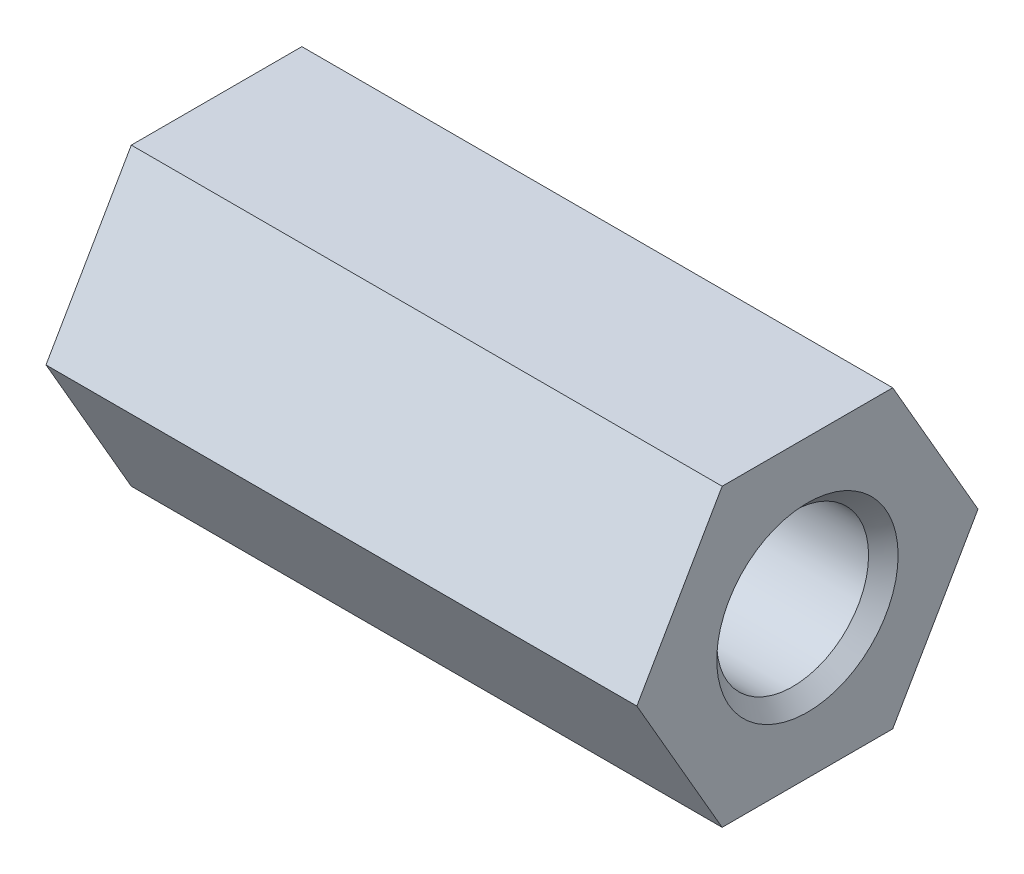
SolidWorks part; units mm, degrees
ref_plane "Front Plane" through (0, 0, 0) normal (0, 0, 1) x (1, 0, 0)
ref_plane "Top Plane" through (0, 0, 0) normal (0, 1, 0) x (1, 0, 0)
ref_plane "Right Plane" through (0, 0, 0) normal (1, 0, 0) x (0, 0, -1)
sketch "Sketch1" plane through (0, 0, 0) normal (1, 0, 0) x (0, 0, -1)
  line L1 (7.3323, 0) -> (3.6662, 6.35)
  line L2 (3.6662, 6.35) -> (-3.6662, 6.35)
  line L3 (-3.6662, 6.35) -> (-7.3323, 0)
  line L4 (-7.3323, 0) -> (-3.6662, -6.35)
  line L5 (-3.6662, -6.35) -> (3.6662, -6.35)
  line L6 (3.6662, -6.35) -> (7.3323, 0)
  circle A0 centre (0, 0) radius 6.35 construction
  point P1 (0, 0)
  dimension "D1" = 12.7
extrude "Boss-Extrude1" add sketch "Sketch1" along normal blind 25.4
hole_wizard "Tap Drill for 5/16-18 Tap1" positions "Sketch2" profile "Sketch3" hole size "5/16-18" standard "ANSI Inch" end condition through all
sketch "Sketch2" plane through (25.4, 0, 0) normal (1, 0, 0) x (0, 0, -1)
  point P0 (0, 0)
sketch "Sketch3" plane through (25.4, 0, 0) normal (0, 1, 0) x (0, 0, -1)
  line L0 (0, 0) -> (0, 25.4)
  line L1 (0, 25.4) -> (3.2639, 25.4)
  line L2 (3.2639, 25.4) -> (3.2639, 0.635)
  line L3 (3.2639, 0.635) -> (3.8989, 0)
  line L5 (3.8989, 0) -> (0, 0)
  line L6 (-3.2639, 0.635) -> (-3.8989, 0) construction
  line L11 (0, -6.35) -> (0, 107.95) construction
  dimension "Thru Hole Dia." = 6.5278
  dimension "Thru Hole Depth" = 25.4
  dimension "Near C'Sink Dia." = 7.7978
  dimension "Near C'Sink Angle" = 90
